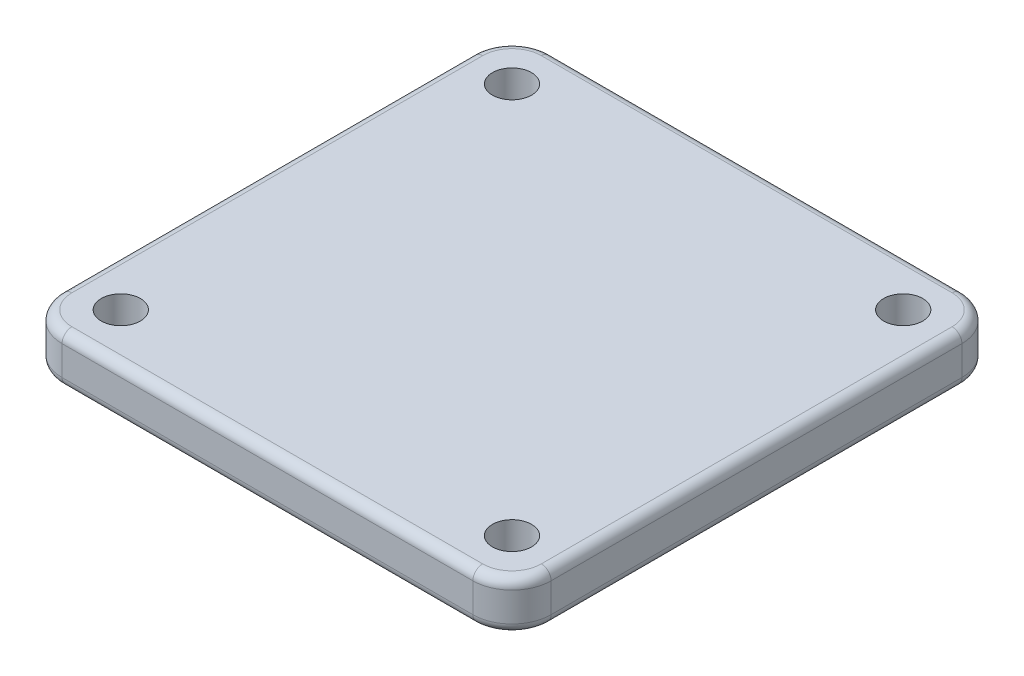
SolidWorks part; units mm, degrees
ref_plane "Front Plane" through (0, 0, 0) normal (0, 0, 1) x (1, 0, 0)
ref_plane "Top Plane" through (0, 0, 0) normal (0, 1, 0) x (1, 0, 0)
ref_plane "Right Plane" through (0, 0, 0) normal (1, 0, 0) x (0, 0, -1)
sketch "Sketch1" plane through (0, 0, 0) normal (0, 1, 0) x (1, 0, 0)
  circle A0 centre (0, 0) radius 5
  circle A1 centre (0, 0) radius 10
  dimension "D1" = 10
  dimension "D2" = 20
extrude "Boss-Extrude1" add sketch "Sketch1" along normal blind 10
sketch "Sketch2" plane through (0, 10, 0) normal (0, 1, 0) x (1, 0, 0)
  line L0 (-20, 20) -> (20, 20) construction
  line L1 (-21, -25) -> (21, -25)
  line L2 (-25, -21) -> (-25, 21)
  line L3 (-21, 25) -> (21, 25)
  line L4 (25, -21) -> (25, 21)
  line L5 (-25, -25) -> (25, 25) construction
  line L6 (-25, 25) -> (25, -25) construction
  line L7 (20, -20) -> (20, 20) construction
  line L8 (-20, -20) -> (20, -20) construction
  line L9 (-20, -20) -> (-20, 20) construction
  line L10 (-25, -25) -> (-25, 25) construction
  line L11 (-25, -25) -> (25, -25) construction
  line L12 (25, -25) -> (25, 25) construction
  line L13 (-25, 25) -> (25, 25) construction
  circle A0 centre (-20, 20) radius 2
  circle A1 centre (20, 20) radius 2
  circle A2 centre (20, -20) radius 2
  circle A3 centre (-20, -20) radius 2
  arc A4 (-25, -21) -> (-21, -25) centre (-21, -21) ccw
  arc A5 (21, -25) -> (25, -21) centre (21, -21) ccw
  arc A6 (25, 21) -> (21, 25) centre (21, 21) ccw
  arc A7 (-21, 25) -> (-25, 21) centre (-21, 21) ccw
  point P0 (0, 0)
  point P20 (0, 0)
  dimension "D4" = 4
  dimension "D6" = 4
  dimension "D1" = 50
  dimension "D2" = 50
  dimension "D3" = 5
  dimension "D5" = 4
extrude "Boss-Extrude2" add sketch "Sketch2" along normal blind 5
sketch "Sketch3" plane through (0, 0, 0) normal (0, 0, 1) x (1, 0, 0)
  circle A0 centre (0, 5) radius 1.5
  point P2 (0, 0)
  dimension "D1" = 3
  dimension "D2" = 5
extrude "Cut-Extrude1" cut sketch "Sketch3" along normal through all
fillet "Fillet1" radius 1 16 edges at (-23.8284, 10, -23.8284) (0, 10, -25) (23.8284, 10, -23.8284) (25, 10, 0) (23.8284, 10, 23.8284) (0, 10, 25) (-23.8284, 10, 23.8284) (-23.8284, 15, -23.8284) (0, 15, -25) (23.8284, 15, -23.8284) (25, 15, 0) (23.8284, 15, 23.8284) (0, 15, 25) (-23.8284, 15, 23.8284) (-25, 10, 0) (-25, 15, 0)
